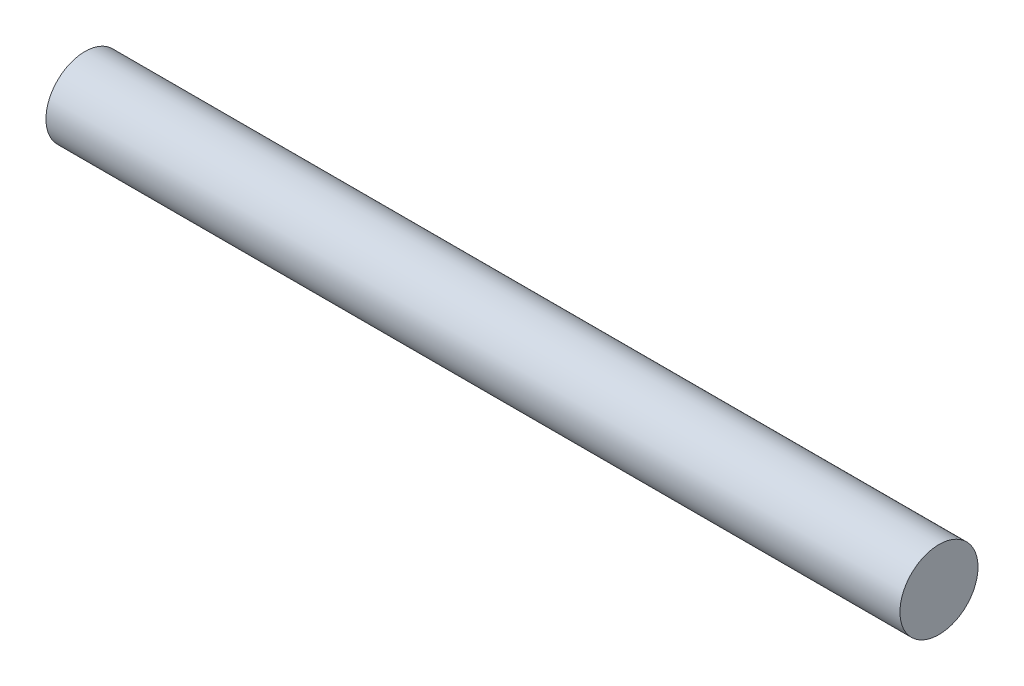
SolidWorks part; units mm, degrees
ref_plane "Front Plane" through (0, 0, 0) normal (0, 0, 1) x (1, 0, 0)
ref_plane "Top Plane" through (0, 0, 0) normal (0, 1, 0) x (1, 0, 0)
ref_plane "Right Plane" through (0, 0, 0) normal (1, 0, 0) x (0, 0, -1)
sketch "Sketch1" plane through (0, 0, 0) normal (1, 0, 0) x (0, 0, -1)
  circle A0 centre (0, 0) radius 1.6
extrude "Boss-Extrude1" add sketch "Sketch1" along normal blind 35
